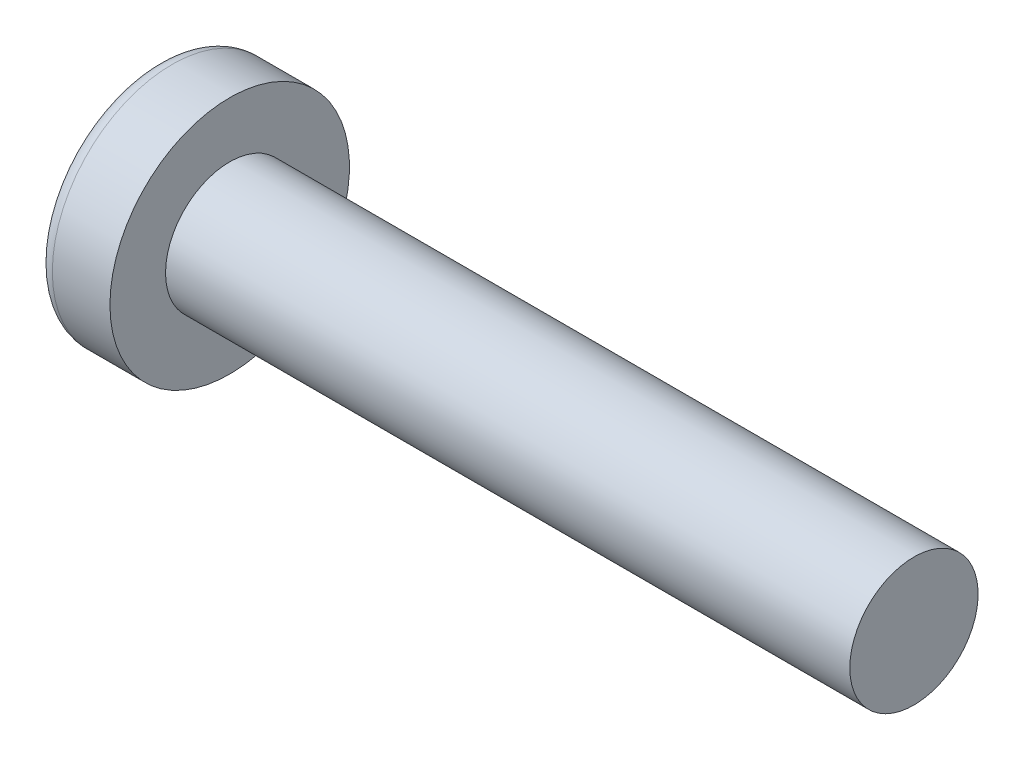
SolidWorks part; units mm, degrees
ref_plane "Plane1" through (0, 0, 0) normal (0, 0, 1) x (1, 0, 0)
ref_plane "Plane2" through (0, 0, 0) normal (0, 1, 0) x (1, 0, 0)
ref_plane "Plane3" through (0, 0, 0) normal (1, 0, 0) x (0, 0, -1)
sketch "BodySke" plane through (0, 0, 0) normal (0, 0, 1) x (1, 0, 0)
  line L0 (2.4, 1.5) -> (2.4, 2.8)
  line L1 (2.9, 6.35) -> (2.9, -3.175) construction
  line L2 (-25.4, 0) -> (127, 0) construction
  line L3 (18.4, 0) -> (0, 0)
  line L4 (2.4, 1.5) -> (18.4, 1.5)
  line L5 (18.4, 1.5) -> (18.4, 0)
  line L6 (1.0534, 2.8) -> (2.4, 2.8)
  line L7 (2.4, -1.5) -> (18.4, -1.5) construction
  line L8 (2.4, 6.35) -> (2.4, -3.175) construction
  arc A0 (0.7472, 2.6293) -> (0, 0) centre (5, 0) ccw
  arc A2 (0.7472, 2.6293) -> (1.0534, 2.8) centre (1.0534, 2.44) cw
revolve "Base-Revolve" add sketch "BodySke" angle 360 about L2
cosmetic thread "ThreadCosmetic" [suppressed] parameters "Thread_length"=15.5, "Thread_minor"=2.439
sketch "Sketch3" plane through (0, 0, 0) normal (1, 0, 0) x (0, 0, -1)
  line L0 (0.37, -1.45) -> (-0.37, -1.45)
  line L1 (0.37, -1.45) -> (0.37, 1.45)
  line L2 (-0.37, 1.45) -> (0.37, 1.45)
  line L3 (-0.37, 1.45) -> (-0.37, -1.45)
ref_plane "Plane4" through (1.76, 0, 0) normal (1, 0, 0) x (0, 0, -1)
sketch "Sketch4" plane through (1.76, 0, 0) normal (1, 0, 0) x (0, 0, -1)
  line L0 (0.185, -0.185) -> (-0.185, -0.185)
  line L1 (0.185, -0.185) -> (0.185, 0.185)
  line L2 (-0.185, 0.185) -> (0.185, 0.185)
  line L3 (-0.185, 0.185) -> (-0.185, -0.185)
loft "Cut-Loft1" cut profiles "Sketch3", "Sketch4"
pattern_circular "CirPattern1" count 2 every 90 about axis through (0, 0, 0) along (1, 0, 0) of "Cut-Loft1"
sketch "ThdSchSke" plane through (0, 0, 0) normal (0, 0, 1) x (1, 0, 0)
  line L0 (2.9, -1.2195) -> (2.7036, -1.5)
  line L1 (2.9, -1.2195) -> (3.0964, -1.5)
  line L2 (3.0964, -1.5) -> (3.0964, -1.875)
  line L3 (-3.175, 0) -> (5.1513, 0) construction
  line L5 (3.0964, -1.875) -> (2.7036, -1.875)
  line L6 (2.7036, -1.875) -> (2.7036, -1.5)
  dimension "SideAngle" = 55
  dimension "VeeAngle" = 70
revolve "ThreadSchematic" [suppressed] cut sketch "ThdSchSke" angle 360 about L3
pattern_linear "ThdSchPat" [suppressed]
equation "\"D1@Sketch3\" = \"Cross_dia@Sketch3\" / 2"
equation "\"D2@Sketch3\" = \"Cross_width@Sketch3\" / 2"
equation "\"D1@Sketch4\" = \"Cross_width@Sketch3\" *.5"
equation "\"D2@Sketch4\" = \"D1@Sketch4\""
equation "\"D3@Sketch4\" = \"D1@Sketch4\" / 2"
equation "\"D4@Sketch4\" = \"D2@Sketch4\" / 2"
equation "\"Thread_length@ThreadCosmetic\" = ((sgn( (\"Length@BodySke\" - \"Advance@BodySke\" ) - \"Thread_nom@BodySke\" )-1)*( (\"Length@BodySke\" - \"Advance@BodySke\" ) - \"Thread_nom@BodySke\" ))/-2+ \"Thread_nom@BodySke\""
equation "\"Thread_minor@ThdSchSke\" = \"Thread_minor@ThreadCosmetic\""
equation "\"Diameter@ThdSchSke\" = \"Diameter@BodySke\""
equation "\"Overcut@ThdSchSke\" = \"Diameter@BodySke\" * 1.25"
equation "\"Start@ThdSchSke\" = \"Head_ht@BodySke\" + \"Length@BodySke\" - \"Thread_length@ThreadCosmetic\"  '---Non-countersunk---"
equation "\"Num_threads@ThdSchPat\" = int( \"Thread_length@ThreadCosmetic\" / \"Advance@BodySke\" + 0.999 )  + 1"
equation "\"Advance@ThdSchPat\" = \"Thread_length@ThreadCosmetic\" /  (\"Num_threads@ThdSchPat\" - 1) 'relax it"
